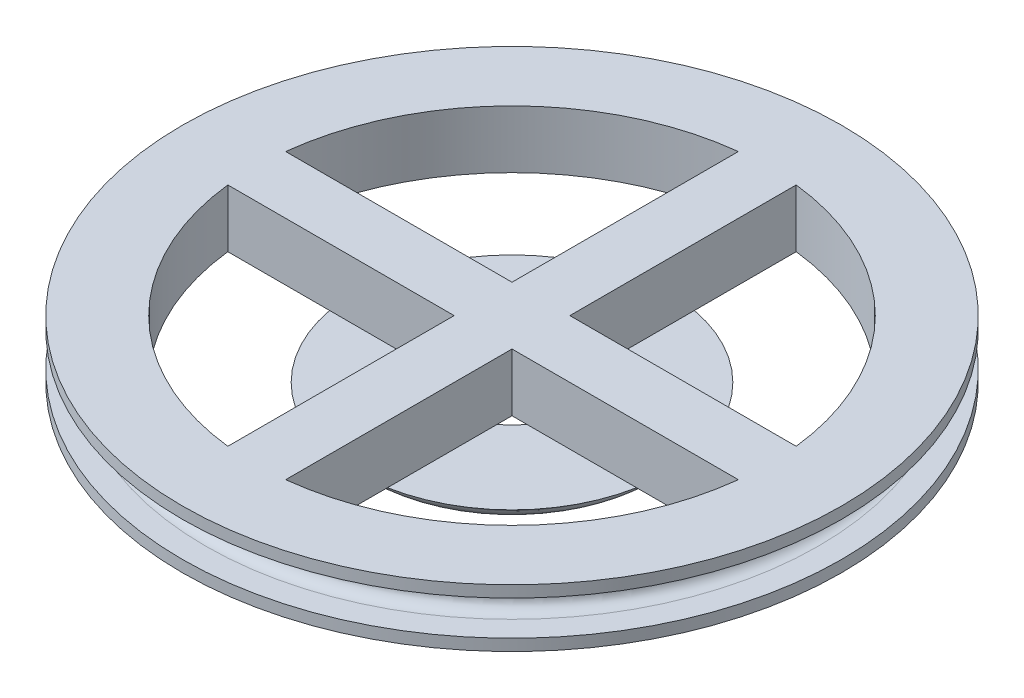
SolidWorks part; units mm, degrees
ref_plane "Front Plane" through (0, 0, 0) normal (0, 0, 1) x (1, 0, 0)
ref_plane "Top Plane" through (0, 0, 0) normal (0, 1, 0) x (1, 0, 0)
ref_plane "Right Plane" through (0, 0, 0) normal (1, 0, 0) x (0, 0, -1)
sketch "Sketch1" plane through (0, 0, 0) normal (0, 1, 0) x (1, 0, 0)
  line L4 (-20, -3.5) -> (-20, 3.5)
  line L5 (-20, 0) -> (-20, -3.5)
  line L6 (-3.5, 20) -> (3.5, 20)
  line L7 (-3.5, 20) -> (-5, 7.5378)
  line L8 (-20, 3.5) -> (-7.5378, 5)
  line L9 (3.5, -20) -> (5, -7.5378)
  line L10 (3.5, 20) -> (5, 7.5378)
  line L11 (-3.5, -20) -> (3.5, -20)
  line L12 (-3.5, -20) -> (-5, -7.5378)
  line L13 (-20, -3.5) -> (-7.5378, -5)
  line L14 (20, -3.5) -> (7.5378, -5)
  line L15 (20, -3.5) -> (20, 3.5)
  line L16 (20, 3.5) -> (7.5378, 5)
  arc A2 (-7.5378, 5) -> (-5, 7.5378) centre (0, 0) cw
  arc A3 (5, 7.5378) -> (7.5378, 5) centre (0, 0) cw
  arc A4 (-5, -7.5378) -> (-7.5378, -5) centre (0, 0) cw
  arc A5 (7.5378, -5) -> (5, -7.5378) centre (0, 0) cw
  circle A6 centre (0, 0) radius 25
extrude "Boss-Extrude2" add sketch "Sketch1" along normal blind 3 contours A6 L14 A5 L9 L11 L12 A4 L13 L4 L8 A2 L7 L6 L10 A3 L16 L15
sketch "Sketch3" plane through (0, 3, 0) normal (0, 1, 0) x (1, 0, 0)
  circle A1 centre (0, 0) radius 57
extrude "Boss-Extrude10" add sketch "Sketch3" along normal blind 2
sketch "Sketch8" plane through (0, 5, 0) normal (0, 1, 0) x (1, 0, 0)
  circle A0 centre (0, 0) radius 51
  circle A1 centre (0, 0) radius 45
extrude "Boss-Extrude11" add sketch "Sketch8" along normal blind 6
sketch "Sketch9" plane through (0, 5, 0) normal (0, 1, 0) x (1, 0, 0)
  circle A0 centre (0, 0) radius 10
extrude "Boss-Extrude12" add sketch "Sketch9" along normal blind 6
sketch "Sketch10" plane through (0, 11, 0) normal (0, 1, 0) x (1, 0, 0)
  circle A0 centre (0, 0) radius 57
extrude "Boss-Extrude13" add sketch "Sketch10" along normal blind 2
fillet "Fillet1" radius 2 1 edges at (0, 11, 51)
fillet "Fillet2" radius 2 1 edges at (0, 5, 51)
fillet "Fillet3" radius 2 1 edges at (0, 3, 25)
fillet "Fillet4" radius 2 1 edges at (0, 0, 25)
sketch "Sketch11" plane through (0, 13, 0) normal (0, 1, 0) x (1, 0, 0)
  circle A0 centre (0, 0) radius 50
extrude "Boss-Extrude14" add sketch "Sketch11" against normal blind 10
sketch "Sketch12" plane through (0, 13, 0) normal (0, 1, 0) x (1, 0, 0)
  line L4 (44.1295, 5) -> (-44.1295, 5)
  line L5 (5, -44.1295) -> (5, 44.1295)
  line L6 (44.1295, -5) -> (-44.1295, -5)
  line L7 (-5, -44.1295) -> (-5, 44.1295)
  circle A0 centre (0, 0) radius 44.4118
extrude "Cut-Extrude3" cut sketch "Sketch12" against normal blind 10 contours L5 A0 L6 | L4 A0 L5 | L7 A0 L4 | L6 A0 L7
